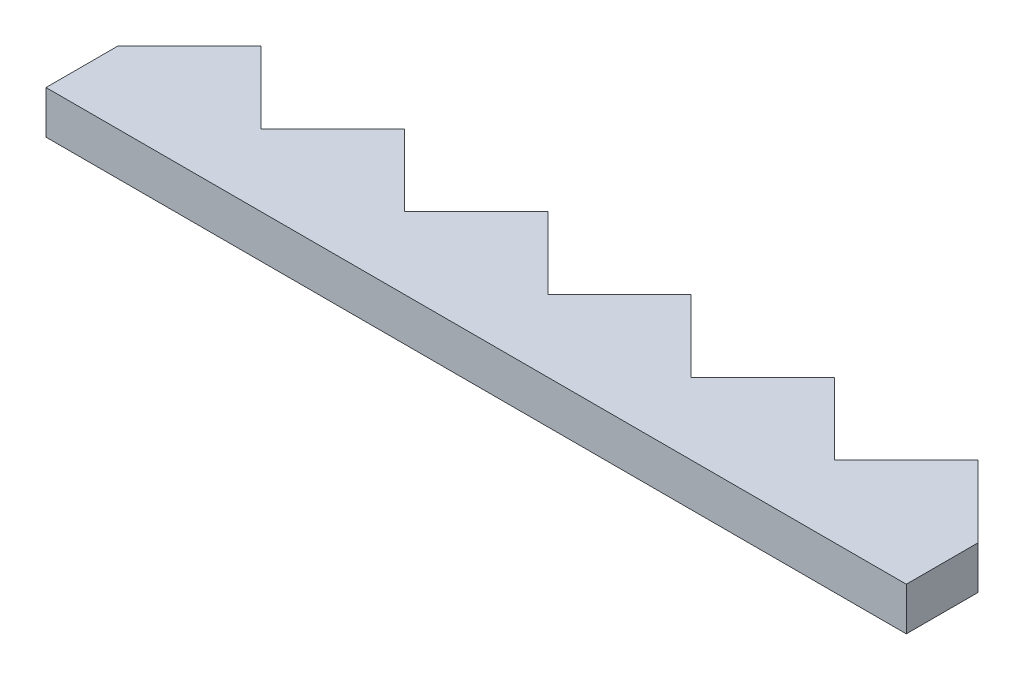
SolidWorks part; units mm, degrees
material "Custom Plastic"
ref_plane "Front Plane" through (0, 0, 0) normal (0, 0, 1) x (1, 0, 0)
ref_plane "Top Plane" through (0, 0, 0) normal (0, 1, 0) x (1, 0, 0)
ref_plane "Right Plane" through (0, 0, 0) normal (1, 0, 0) x (0, 0, -1)
sketch "Sketch1" plane through (0, 0, 0) normal (0, 1, 0) x (1, 0, 0)
  line L0 (0, 5) -> (5, 10)
  line L2 (0, 5) -> (0, 0)
  line L3 (0, 0) -> (60, 0)
  line L5 (5, 10) -> (10, 5)
  line L6 (10, 5) -> (15, 10)
  line L7 (15, 10) -> (20, 5)
  line L8 (20, 5) -> (25, 10)
  line L9 (25, 10) -> (30, 5)
  line L10 (30, 5) -> (35, 10)
  line L11 (35, 10) -> (40, 5)
  line L12 (40, 5) -> (45, 10)
  line L13 (45, 10) -> (50, 5)
  line L18 (5, 10) -> (65, 10) construction
  line L20 (50, 5) -> (55, 10)
  line L21 (55, 10) -> (60, 5)
  line L22 (60, 0) -> (60, 5)
  dimension "D1" = 5
  dimension "D2" = 10
  dimension "D4" = 10
  dimension "D5" = 6
extrude "Boss-Extrude1" add sketch "Sketch1" along normal blind 3
